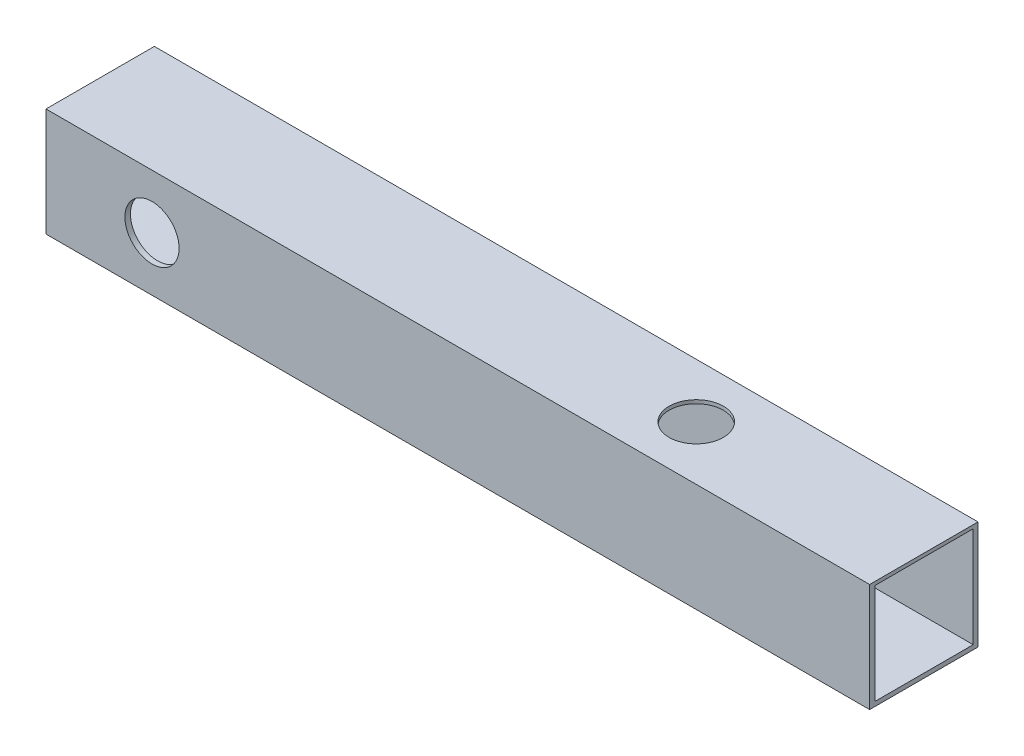
SolidWorks part; units mm, degrees
ref_plane "Front Plane" through (0, 0, 0) normal (0, 0, 1) x (1, 0, 0)
ref_plane "Top Plane" through (0, 0, 0) normal (0, 1, 0) x (1, 0, 0)
ref_plane "Right Plane" through (0, 0, 0) normal (1, 0, 0) x (0, 0, -1)
sketch "Sketch1" plane through (0, 0, 0) normal (0, 1, 0) x (1, 0, 0)
  line L1 (-38, 5) -> (38, 5)
  line L2 (-38, 5) -> (-38, -5)
  line L3 (-38, -5) -> (38, -5)
  line L4 (38, 5) -> (38, -5)
  line L5 (-38, 5) -> (38, -5) construction
  line L6 (-38, -5) -> (38, 5) construction
  point P0 (0, 0)
  dimension "D1" = 10
  dimension "76" = 76
extrude "Boss-Extrude1" add sketch "Sketch1" along normal blind 10
sketch "Sketch2" plane through (-38, 0, 0) normal (-1, 0, 0) x (0, 0, 1)
  line L1 (-4.5557, 0.4105) -> (4.4907, 0.4105)
  line L2 (-4.5557, 0.4105) -> (-4.5557, 9.6745)
  line L3 (-4.5557, 9.6745) -> (4.4907, 9.6745)
  line L4 (4.4907, 0.4105) -> (4.4907, 9.6745)
  line L5 (-4.5557, 0.4105) -> (4.4907, 9.6745) construction
  line L6 (-4.5557, 9.6745) -> (4.4907, 0.4105) construction
  point P0 (-0.0325, 5.0425)
  point P5 (0, 0)
  point P6 (0, 0)
extrude "Cut-Extrude1" cut sketch "Sketch2" against normal through all
sketch "Sketch4" plane through (0, 0, 5) normal (0, 0, 1) x (1, 0, 0)
  line L0 (-28.2187, 5) -> (16.7813, 5)
  circle A0 centre (-28.2187, 5) radius 2.5
  dimension "D1" = 5
extrude "Cut-Extrude2" cut sketch "Sketch4" against normal blind 76
sketch "Sketch6" plane through (0, 10, 0) normal (0, 1, 0) x (1, 0, 0)
  line L1 (38, -5) -> (38, 5) construction
  circle A0 centre (17, 0) radius 2.5
  dimension "D1" = 5
  dimension "D2" = 21
extrude "Cut-Extrude3" cut sketch "Sketch6" against normal blind 76
